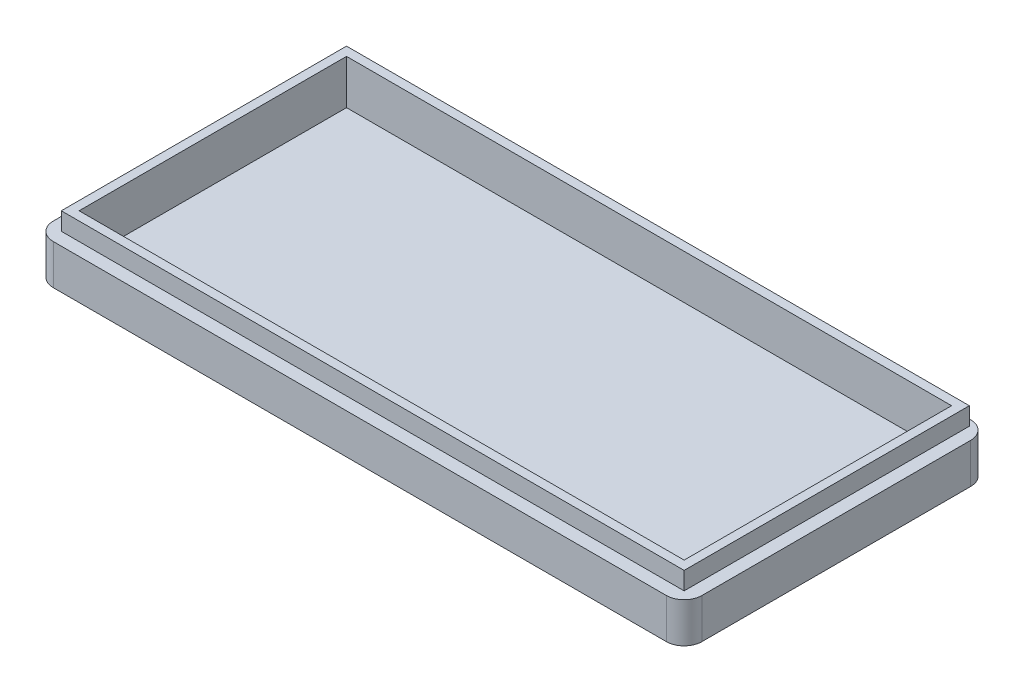
SolidWorks part; units mm, degrees
ref_plane "Front Plane" through (0, 0, 0) normal (0, 0, 1) x (1, 0, 0)
ref_plane "Top Plane" through (0, 0, 0) normal (0, 1, 0) x (1, 0, 0)
ref_plane "Right Plane" through (0, 0, 0) normal (1, 0, 0) x (0, 0, -1)
sketch "Sketch1" plane through (0, 0, 0) normal (0, 1, 0) x (1, 0, 0)
  line L1 (-36.9148, -18.3883) -> (36.0852, -18.3883)
  line L2 (-36.9148, -18.3883) -> (-36.9148, 15.8617)
  line L3 (-36.9148, 15.8617) -> (36.0852, 15.8617)
  line L4 (36.0852, -18.3883) -> (36.0852, 15.8617)
  dimension "D1" = 73
  dimension "D2" = 34.25
extrude "Boss-Extrude1" add sketch "Sketch1" along normal blind 4.5
fillet "Fillet1" radius 2 4 edges at (36.0852, 2.25, -15.8617) (36.0852, 2.25, 18.3883) (-36.9148, 2.25, 18.3883) (-36.9148, 2.25, -15.8617)
sketch "Sketch2" plane through (0, 4.5, 0) normal (0, 1, 0) x (1, 0, 0)
  line L0 (-34.9148, -18.3883) -> (34.0852, -18.3883) construction
  line L1 (-35.4648, -16.9383) -> (34.6352, -16.9383)
  line L2 (-35.4648, -16.9383) -> (-35.4648, 15.1617)
  line L3 (-35.4648, 15.1617) -> (34.6352, 15.1617)
  line L4 (34.6352, -16.9383) -> (34.6352, 15.1617)
  line L5 (34.0852, 15.8617) -> (-34.9148, 15.8617) construction
  line L6 (-36.9148, 13.8617) -> (-36.9148, -16.3883) construction
  line L7 (36.0852, -16.3883) -> (36.0852, 13.8617) construction
  line L9 (-34.4648, -15.9383) -> (33.6352, -15.9383)
  line L10 (-34.4648, -15.9383) -> (-34.4648, 14.1617)
  line L11 (-34.4648, 14.1617) -> (33.6352, 14.1617)
  line L12 (33.6352, -15.9383) -> (33.6352, 14.1617)
  dimension "D1" = 1.45
  dimension "D2" = 0.7
  dimension "D3" = 1.45
  dimension "D4" = 1.45
  dimension "D5" = 1
  dimension "D6" = 1
  dimension "D7" = 1
  dimension "D8" = 1
extrude "Boss-Extrude2" add sketch "Sketch2" along normal blind 2
sketch "Sketch3" plane through (0, 4.5, 0) normal (0, 1, 0) x (1, 0, 0)
  line L1 (-34.4648, 14.1617) -> (33.6352, 14.1617)
  line L2 (-34.4648, 14.1617) -> (-34.4648, -15.9383)
  line L3 (-34.4648, -15.9383) -> (33.6352, -15.9383)
  line L4 (33.6352, 14.1617) -> (33.6352, -15.9383)
extrude "Cut-Extrude1" cut sketch "Sketch3" against normal blind 3 from surface at 0 starting at face at (-0.4148, 4.5, 0.8883)
